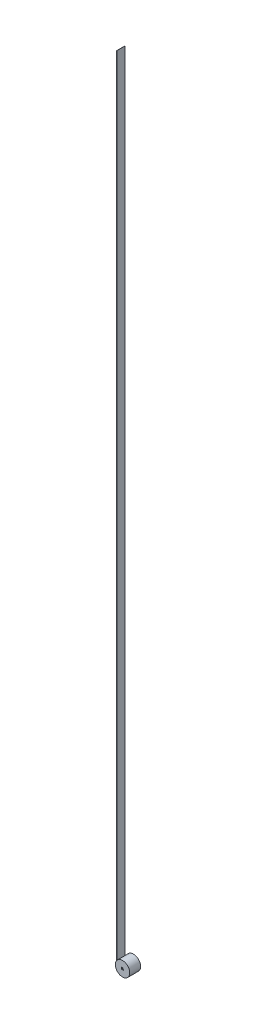
SolidWorks part; units mm, degrees
ref_plane "Front" through (0, 0, 0) normal (0, 0, 1) x (1, 0, 0)
ref_plane "Top" through (0, 0, 0) normal (0, 1, 0) x (1, 0, 0)
ref_plane "Right" through (0, 0, 0) normal (1, 0, 0) x (0, 0, -1)
sketch "Sketch1" plane through (0, 0, 0) normal (0, 0, 1) x (1, 0, 0)
  circle A0 centre (0, 0) radius 28.25
  dimension "D1" = 56.5
extrude "Boss-Extrude1" add sketch "Sketch1" along normal blind 43
sketch "Sketch4" plane through (0, 0, 0) normal (0, 1, 0) x (1, 0, 0)
  line L0 (-28.25, -5.625) -> (-28.25, -37.375)
  line L1 (-28.25, -37.375) -> (-28.65, -37.375)
  line L2 (-28.65, -37.375) -> (-28.65, -5.625)
  line L3 (-28.65, -5.625) -> (-28.25, -5.625)
  line L4 (28.25, 0) -> (-28.25, 0) construction
  dimension "D1" = 31.75
  dimension "D2" = 5.625
  dimension "D3" = 0.4
extrude "Boss-Extrude2" add sketch "Sketch4" along normal blind 3106 separate body
sketch "Sketch6" plane through (0, 0, 43) normal (0, 0, 1) x (1, 0, 0)
  line L5 (4, -4) -> (-4, -4)
  line L6 (4, -4) -> (4, 4)
  line L7 (4, 4) -> (-4, 4)
  line L8 (-4, -4) -> (-4, 4)
  line L9 (4, -4) -> (-4, 4) construction
  line L10 (4, 4) -> (-4, -4) construction
  point P0 (0, 0)
  dimension "D1" = 8
extrude "Cut-Extrude1" cut sketch "Sketch6" against normal blind 3.5
